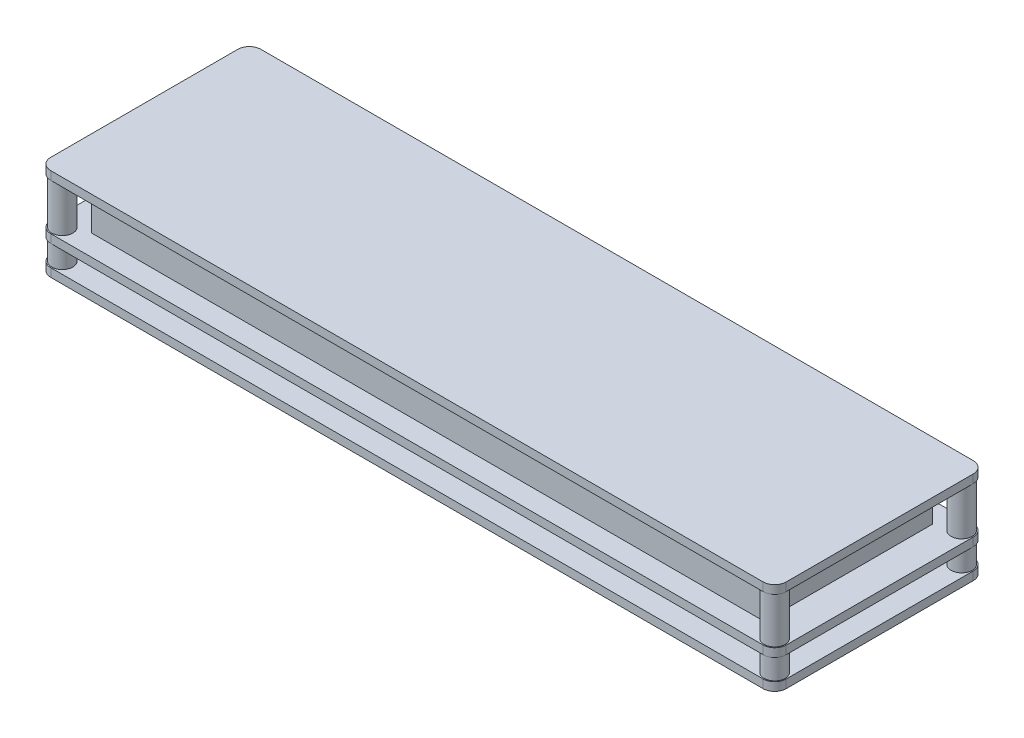
SolidWorks part; units mm, degrees
ref_plane "Front Plane" through (0, 0, 0) normal (0, 0, 1) x (1, 0, 0)
ref_plane "Top Plane" through (0, 0, 0) normal (0, 1, 0) x (1, 0, 0)
ref_plane "Right Plane" through (0, 0, 0) normal (1, 0, 0) x (0, 0, -1)
sketch "Sketch1" plane through (0, 0, 0) normal (0, 1, 0) x (1, 0, 0)
  line L1 (87.5, -25) -> (-87.5, -25)
  line L2 (87.5, -25) -> (87.5, 25)
  line L3 (87.5, 25) -> (-87.5, 25)
  line L4 (-87.5, -25) -> (-87.5, 25)
  line L5 (87.5, -25) -> (-87.5, 25) construction
  line L6 (87.5, 25) -> (-87.5, -25) construction
  point P0 (0, 0)
  dimension "D1" = 50
  dimension "D2" = 175
extrude "Boss-Extrude1" add sketch "Sketch1" along normal blind 2
sketch "Sketch2" plane through (0, 2, 0) normal (0, 1, 0) x (1, 0, 0)
  line L4 (-87.5, 25) -> (-87.5, -25)
  line L5 (-87.5, -25) -> (87.5, -25)
  line L6 (87.5, -25) -> (87.5, 25)
  line L7 (87.5, 25) -> (-87.5, 25)
  line L8 (-87.5, 25) -> (-87.5, -25)
  line L9 (-87.5, -25) -> (87.5, -25)
  line L10 (87.5, -25) -> (87.5, 25)
  line L11 (87.5, 25) -> (-87.5, 25)
  dimension "D1" = 0
extrude "Boss-Extrude2" add sketch "Sketch2" along normal blind 2 from offset 11 separate body
sketch "Sketch3" plane through (0, 0, 0) normal (0, -1, 0) x (1, 0, 0)
  line L4 (-87.5, 25) -> (-87.5, -25)
  line L5 (-87.5, -25) -> (87.5, -25)
  line L6 (87.5, -25) -> (87.5, 25)
  line L7 (87.5, 25) -> (-87.5, 25)
  line L8 (-87.5, 25) -> (-87.5, -25)
  line L9 (-87.5, -25) -> (87.5, -25)
  line L10 (87.5, -25) -> (87.5, 25)
  line L11 (87.5, 25) -> (-87.5, 25)
  dimension "D1" = 0
extrude "Boss-Extrude3" add sketch "Sketch3" along normal blind 2 from offset 5 separate body
sketch "Sketch5" plane through (0, 2, 0) normal (0, 1, 0) x (1, 0, 0)
  line L1 (-80, -20) -> (80, -20)
  line L2 (-80, -20) -> (-80, 20)
  line L3 (-80, 20) -> (80, 20)
  line L4 (80, -20) -> (80, 20)
  line L5 (-80, -20) -> (80, 20) construction
  line L6 (-80, 20) -> (80, -20) construction
  point P0 (0, 0)
  dimension "D1" = 160
  dimension "D2" = 40
extrude "Boss-Extrude4" add sketch "Sketch5" along normal blind 10
sketch "Sketch7" plane through (0, 12, 0) normal (0, 1, 0) x (1, 0, 0)
  line L1 (-72.5, -17.5) -> (-77.5, -17.5)
  line L2 (-72.5, -17.5) -> (-72.5, 17.5)
  line L3 (-72.5, 17.5) -> (-77.5, 17.5)
  line L4 (-77.5, -17.5) -> (-77.5, 17.5)
  line L5 (-72.5, -17.5) -> (-77.5, 17.5) construction
  line L6 (-72.5, 17.5) -> (-77.5, -17.5) construction
  point P0 (-75, 0)
  dimension "D1" = 5
  dimension "D2" = 35
  dimension "D3" = 75
extrude "Cut-Extrude1" cut sketch "Sketch7" against normal blind 0.1
pattern_linear "LPattern1" count 16 spacing 10 along (1, 0, 0) of "Cut-Extrude1"
sketch "Sketch8" plane through (0, -5, 0) normal (0, 1, 0) x (1, 0, 0)
  line L0 (-87.5, -25) -> (-87.5, 25) construction
  line L2 (-87.5, 25) -> (87.5, 25) construction
  line L3 (87.5, 25) -> (-87.5, 25) construction
  line L4 (-87.5, 25) -> (-87.5, -25) construction
  circle A0 centre (-84.75, 22.25) radius 2.5
  circle A1 centre (-84.75, 22.25) radius 2.75 construction
  dimension "D1" = 5
  dimension "D3" = 5.5
  dimension "D2" = 90
extrude "Boss-Extrude5" add sketch "Sketch8" along normal up to surface (18 mm away) up to face at (0, 13, 0)
mirror "Mirror1" about plane through (0, 0, 0) normal (1, 0, 0) of "Boss-Extrude5" second plane through (0, 0, 0) second plane normal (0, 0, 1)
fillet "Fillet2" radius 2.75 12 edges at (-87.5, 14, 25) (-87.5, 1, 25) (-87.5, -6, 25) (87.5, -6, 25) (87.5, 1, 25) (87.5, 14, 25) (87.5, 14, -25) (87.5, 1, -25) (87.5, -6, -25) (-87.5, -6, -25) (-87.5, 1, -25) (-87.5, 14, -25)
